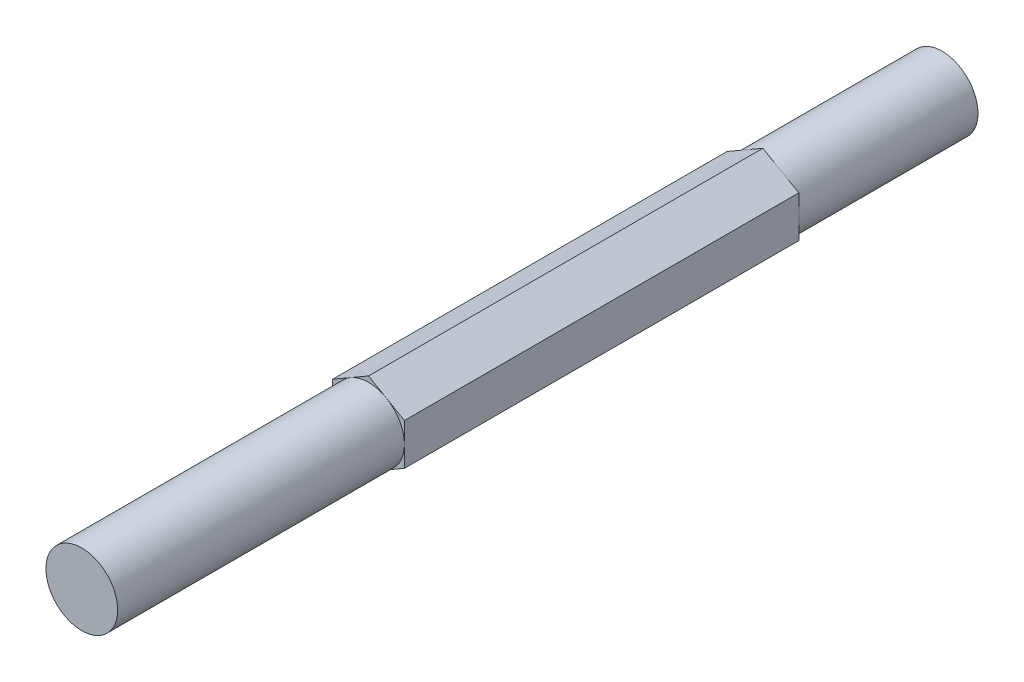
SolidWorks part; units mm, degrees
ref_plane "Front Plane" through (0, 0, 0) normal (0, 0, 1) x (1, 0, 0)
ref_plane "Top Plane" through (0, 0, 0) normal (0, 1, 0) x (1, 0, 0)
ref_plane "Right Plane" through (0, 0, 0) normal (1, 0, 0) x (0, 0, -1)
sketch "Sketch2" plane through (0, 0, 0) normal (0, 0, 1) x (1, 0, 0)
  line L1 (0, 3.6662) -> (-3.175, 1.8331)
  line L2 (-3.175, 1.8331) -> (-3.175, -1.8331)
  line L3 (-3.175, -1.8331) -> (0, -3.6662)
  line L4 (0, -3.6662) -> (3.175, -1.8331)
  line L5 (3.175, -1.8331) -> (3.175, 1.8331)
  line L6 (3.175, 1.8331) -> (0, 3.6662)
  circle A0 centre (0, 0) radius 3.175 construction
  point P10 (0, 0)
  dimension "D1" = 6.35
extrude "Boss-Extrude1" add sketch "Sketch2" along normal blind 76.2
sketch "Sketch3" plane through (0, 0, 76.2) normal (0, 0, 1) x (1, 0, 0)
  circle A0 centre (0, 0) radius 3.175
  dimension "D1" = 6.35
extrude "Cut-Extrude1" cut sketch "Sketch3" against normal blind 25.4 flip side to cut
sketch "Sketch4" plane through (0, 0, 0) normal (0, 0, -1) x (-1, 0, 0)
  line L0 (0, 3.6662) -> (3.175, 1.8331) construction
  circle A0 centre (0, 0) radius 3.175
  point P5 (1.5875, 2.7496)
extrude "Cut-Extrude2" cut sketch "Sketch4" against normal blind 15.875 flip side to cut
